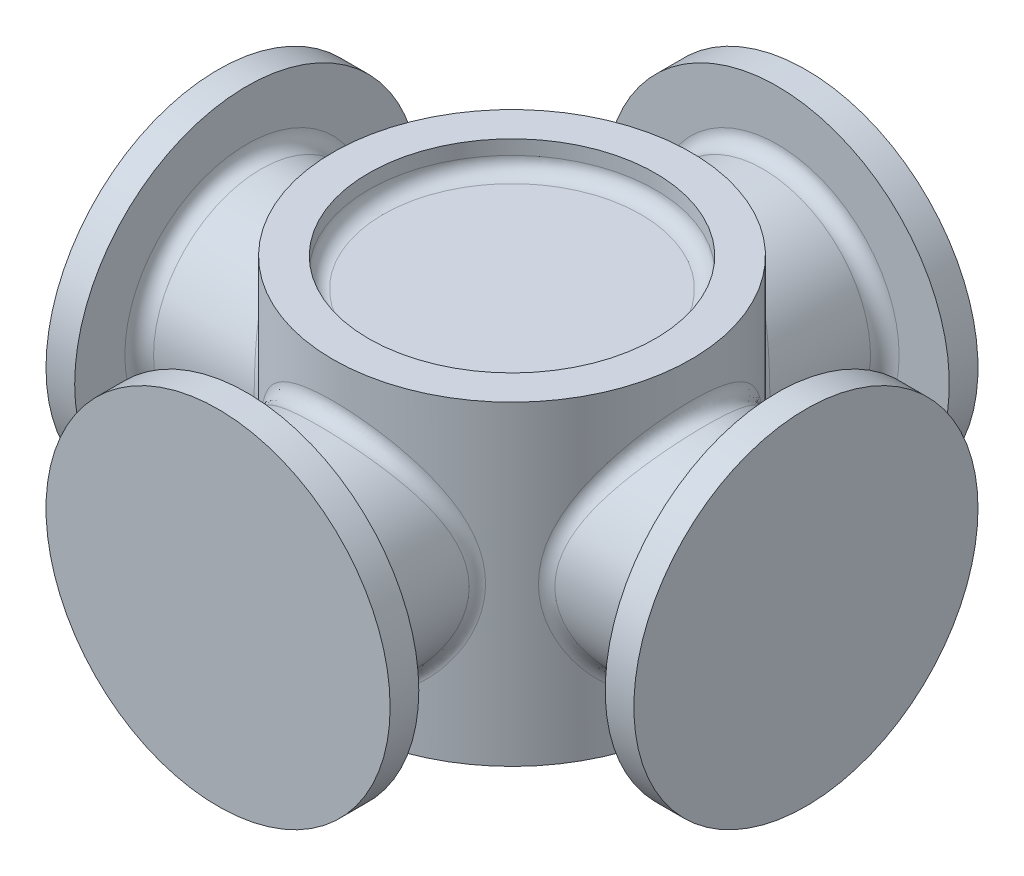
SolidWorks part; units mm, degrees
other "Markup1"
sketch "Sketch8" plane through (-26.035, 29.21, 26.035) normal (-0.5159, 0.33, 0.7905) x (0.8131, -0.102, 0.5732)
ref_plane "Front Plane" through (0, 0, 0) normal (0, 0, 1) x (1, 0, 0)
ref_plane "Top Plane" through (0, 0, 0) normal (0, 1, 0) x (1, 0, 0)
ref_plane "Right Plane" through (0, 0, 0) normal (1, 0, 0) x (0, 0, -1)
sketch "Sketch3" plane through (0, 0, 0) normal (0, 1, 0) x (1, 0, 0)
  circle A0 centre (0, 0) radius 15.875
  dimension "D1" = 31.75
extrude "Boss-Extrude2" add sketch "Sketch3" along normal blind 27.94
ref_plane "Plane1" through (0, 0, 15.875) normal (0, 0, 1) x (1, 0, 0)
sketch "Sketch4" plane through (0, 0, 15.875) normal (0, 0, 1) x (1, 0, 0)
  line L0 (0, -16.764) -> (0, 16.764) construction
  line L1 (28.6385, 0) -> (-28.6385, 0) construction
  circle A0 centre (0, 13.97) radius 9.525
  dimension "D1" = 19.05
  dimension "D2" = 13.97
extrude "Boss-Extrude3" add sketch "Sketch4" along normal blind 10.16 and the other way up to surface contours A0
sketch "Sketch5" plane through (0, 0, 26.035) normal (0, 0, 1) x (1, 0, 0)
  circle A0 centre (0, 13.97) radius 15.24
  circle A1 centre (0, 13.97) radius 9.525 construction
  dimension "D1" = 30.48
extrude "Boss-Extrude4" add sketch "Sketch5" against normal blind 2.54 contours A0
pattern_circular "CirPattern1" count 4 over 360 about axis through (0, 0, 0) along (0, 1, 0) of "Boss-Extrude3", "Boss-Extrude4"
fillet "Fillet1" radius 1.27 4 edges at (9.525, 13.9494, 12.7) (12.7, 13.9494, -9.525) (-12.7, 13.9494, 9.525) (-2.5578, 4.7949, -15.6676)
fillet "Fillet2" radius 1.27 4 edges at (-9.525, 13.97, -23.495) (23.495, 13.97, -9.525) (9.525, 13.97, 23.495) (-23.495, 13.97, 9.525)
sketch "Sketch6" plane through (0, 27.94, 0) normal (0, 1, 0) x (1, 0, 0)
  circle A0 centre (0, 0) radius 12.7
  dimension "D1" = 25.4
extrude "Cut-Extrude1" cut sketch "Sketch6" against normal blind 2.54
fillet "Fillet3" radius 1.27 1 edges at (0, 25.4, 12.7)
sketch "Sketch7" plane through (0, 0, 0) normal (0, -1, 0) x (1, 0, 0)
  circle A0 centre (0, 0) radius 12.7
  dimension "D1" = 25.4
extrude "Cut-Extrude2" cut sketch "Sketch7" against normal blind 2.54
fillet "Fillet4" radius 1.27 1 edges at (0, 2.54, -12.7)
equation "\"D1@Boss-Extrude3\"=(2.05/2)-0.625"
